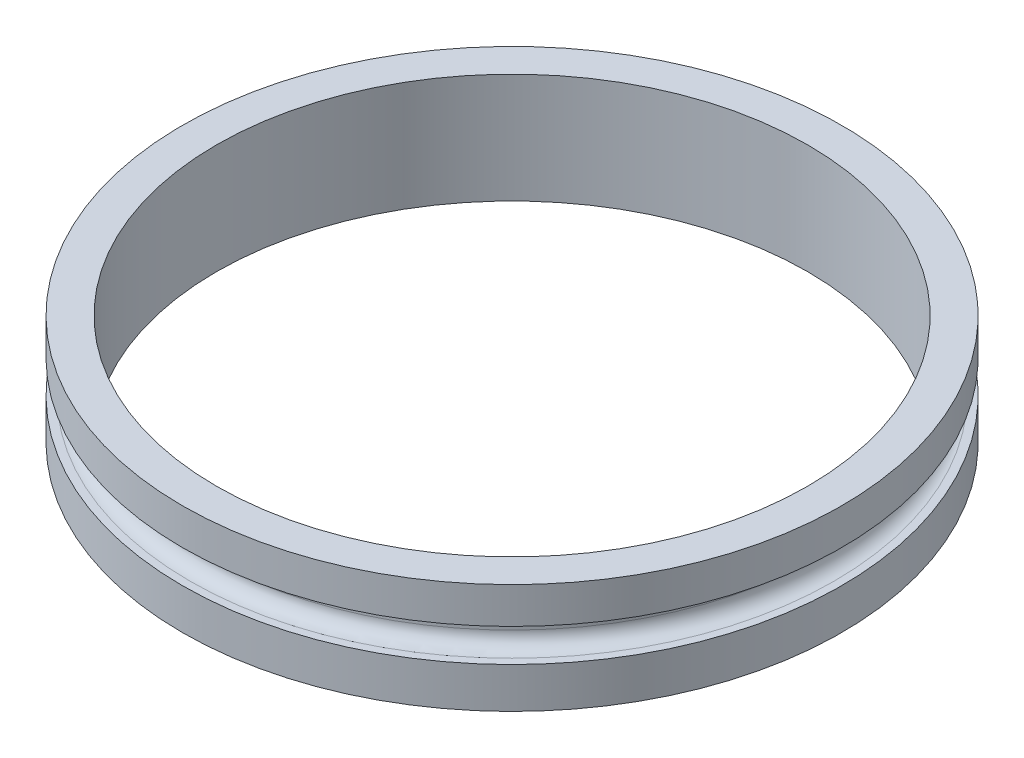
SolidWorks part; units mm, degrees
material "PLA"
ref_plane "Front Plane" through (0, 0, 0) normal (0, 0, 1) x (1, 0, 0)
ref_plane "Top Plane" through (0, 0, 0) normal (0, 1, 0) x (1, 0, 0)
ref_plane "Right Plane" through (0, 0, 0) normal (1, 0, 0) x (0, 0, -1)
sketch "Sketch1" plane through (0, 0, 0) normal (0, 0, 1) x (1, 0, 0)
  line L0 (34.1757, 0) -> (34.1757, 12.7)
  line L1 (34.1757, 12.7) -> (38.1, 12.7)
  line L2 (38.1, 12.7) -> (38.1, 8.509)
  line L3 (38.1, 8.509) -> (35.56, 8.509)
  line L4 (35.56, 8.509) -> (35.56, 4.699)
  line L5 (35.56, 4.699) -> (38.1, 4.699)
  line L6 (38.1, 4.699) -> (38.1, 0)
  line L7 (38.1, 0) -> (34.1757, 0)
  dimension "D2" = 3.81
  dimension "D3" = 12.7
  dimension "D4" = 4.191
  dimension "D5" = 2.54
  dimension "D6" = 1.3843
  dimension "D1" = 38.1
ref_axis "Axis1" through (0, 13.335, 0) along (0, -1, 0)
revolve "Revolve1" add sketch "Sketch1" angle 360 about axis through (0, 13.335, 0) along (0, -1, 0)
fillet "Fillet1" radius 1.651 2 edges at (0, 4.699, 35.56) (0, 8.509, 35.56)
equation "\"D1@Sketch1\"=(3.01-\"tolerance_body tube\")/2"
equation "\"tolerance_body tube\"= 0.01"
